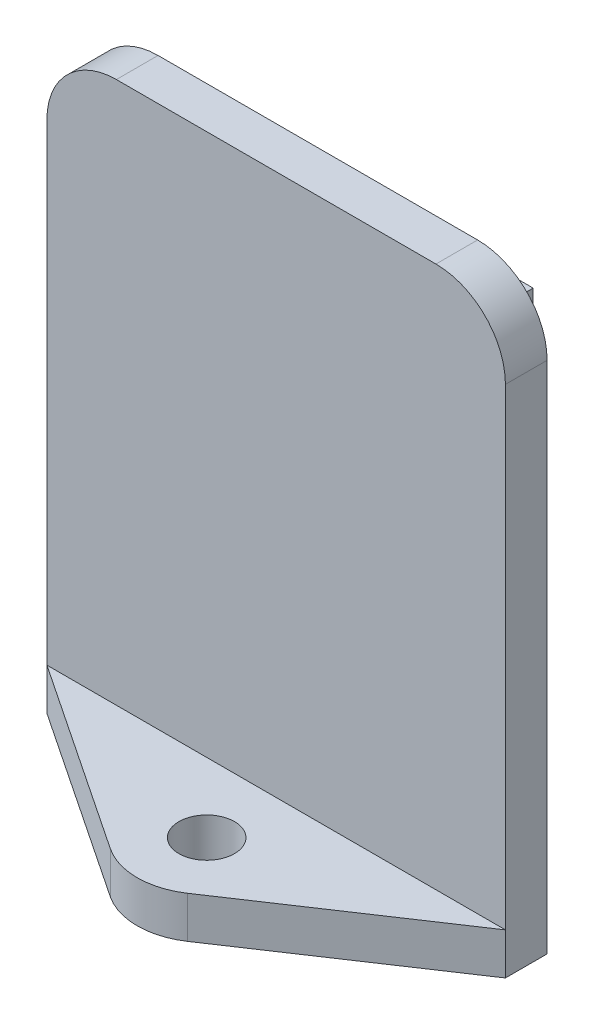
SolidWorks part; units mm, degrees
ref_plane "前视基准面" through (0, 0, 0) normal (0, 0, 1) x (1, 0, 0)
ref_plane "上视基准面" through (0, 0, 0) normal (0, 1, 0) x (1, 0, 0)
ref_plane "右视基准面" through (0, 0, 0) normal (1, 0, 0) x (0, 0, -1)
sketch "草图1" plane through (0, 0, 0) normal (0, 0, 1) x (1, 0, 0)
  line L1 (11.5, 23.5) -> (-11.5, 23.5)
  line L2 (16.5, 18.5) -> (16.5, -18.5)
  line L3 (16.5, -18.5) -> (-16.5, -18.5)
  line L4 (-16.5, 18.5) -> (-16.5, -18.5)
  line L5 (0, -18.5) -> (0, 23.5) construction
  line L6 (16.5, 0) -> (-16.5, 0) construction
  arc A0 (11.5, 23.5) -> (16.5, 18.5) centre (11.5, 18.5) cw
  arc A1 (-11.5, 23.5) -> (-16.5, 18.5) centre (-11.5, 18.5) ccw
  point P0 (0, 0)
  point P6 (16.5, 23.5)
  point P9 (-16.5, 23.5)
  dimension "D3" = 5
  dimension "D1" = 33
  dimension "D2" = 42
extrude "凸台-拉伸1" add sketch "草图1" along normal blind 3
sketch "草图2" plane through (0, -18.5, 0) normal (0, -1, 0) x (1, 0, 0)
  line L1 (55, 0) -> (-55, 0) construction
  line L2 (0, 0) -> (0, -4.2239) construction
  line L3 (-16.5, 3) -> (16.5, 3) construction
  line L4 (-2.7754, 12.159) -> (-16.5, 3)
  line L5 (2.7754, 12.159) -> (16.5, 3)
  circle A0 centre (0, 8) radius 2
  circle A1 centre (0, 8) radius 5
  line M5 (16.5, 3) -> (-16.5, 3)
  dimension "D2" = 4
  dimension "D1" = 8
extrude "凸台-拉伸2" add sketch "草图2" against normal blind 3 contours L2 A1 A0 | A1 L2 A0 | A1 L4 M5 | A1 L5 M5
sketch "草图3" plane through (0, 0, 0) normal (0, 0, -1) x (-1, 0, 0)
  line L0 (16.5, -18.5) -> (-16.5, -18.5) construction
  line L1 (-13.5, -18.5) -> (13.5, -18.5)
  line L2 (-13.5, -18.5) -> (-13.5, 20.5)
  line L3 (-13.5, 20.5) -> (13.5, 20.5)
  line L4 (13.5, -18.5) -> (13.5, 20.5)
  line L5 (-16.5, -18.5) -> (-16.5, 18.5) construction
  line L6 (16.5, 18.5) -> (16.5, -18.5) construction
  line L7 (-11.5, 23.5) -> (11.5, 23.5) construction
  dimension "D1" = 3
  dimension "D2" = 3
  dimension "D3" = 3
extrude "凸台-拉伸3" add sketch "草图3" along normal blind 2
